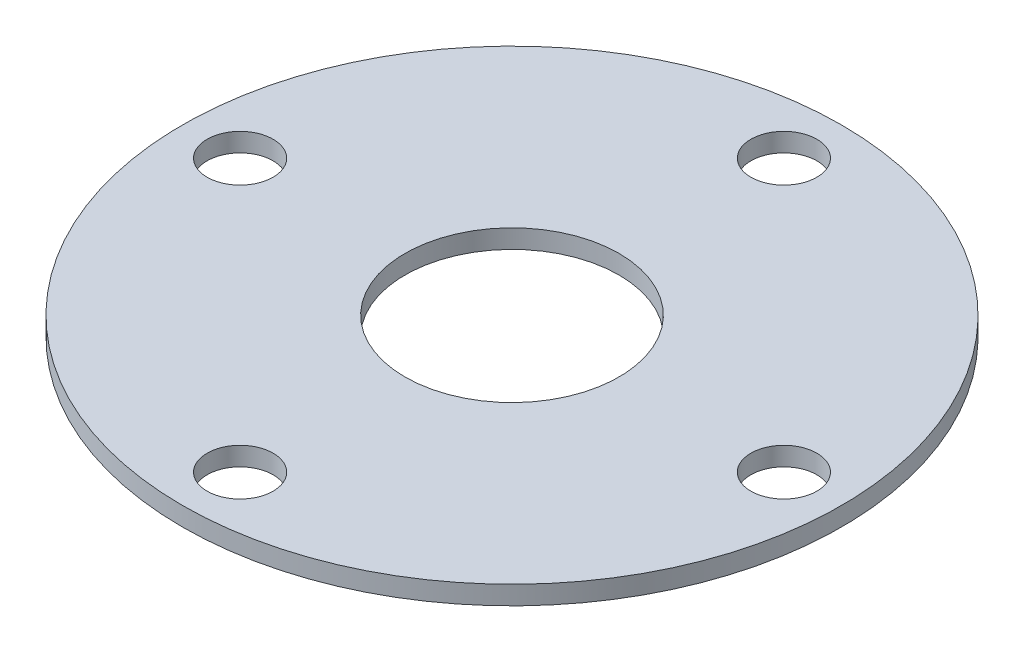
SolidWorks part; units mm, degrees
material "PVC Rigid"
ref_plane "Front Plane" through (0, 0, 0) normal (0, 0, 1) x (1, 0, 0)
ref_plane "Top Plane" through (0, 0, 0) normal (0, 1, 0) x (1, 0, 0)
ref_plane "Right Plane" through (0, 0, 0) normal (1, 0, 0) x (0, 0, -1)
sketch "Sketch1" plane through (0, 0, 0) normal (0, 1, 0) x (1, 0, 0)
  circle A0 centre (0, 0) radius 31.75
  circle A1 centre (0, 0) radius 10.3124
  circle A3 centre (0, -26.1938) radius 3.175
  circle A4 centre (-26.1938, 0) radius 3.175
  circle A5 centre (0, 26.1938) radius 3.175
  circle A6 centre (26.1938, 0) radius 3.175
  dimension "D1" = 4
  dimension "OD" = 63.5
  dimension "D2" = 6.35
extrude "Boss-Extrude1" add sketch "Sketch1" along normal blind 1.8034
